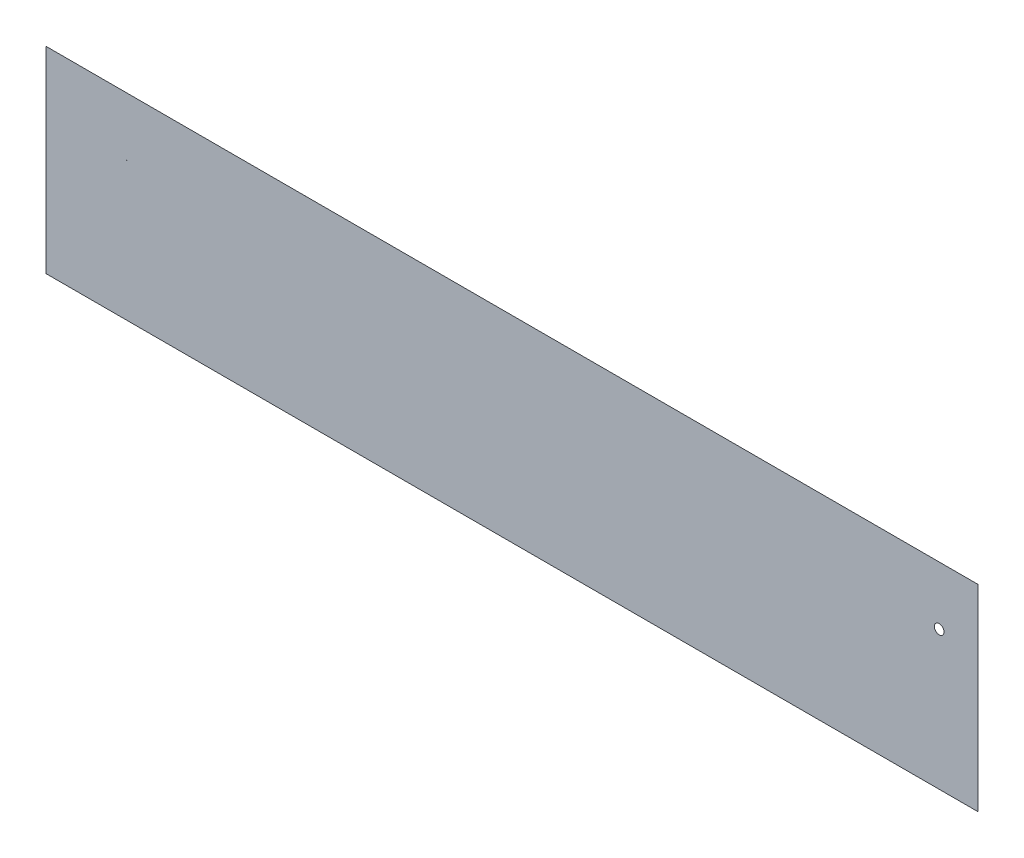
SolidWorks part; units mm, degrees
ref_plane "Front" through (0, 0, 0) normal (0, 0, 1) x (1, 0, 0)
ref_plane "Top" through (0, 0, 0) normal (0, 1, 0) x (1, 0, 0)
ref_plane "Right" through (0, 0, 0) normal (1, 0, 0) x (0, 0, -1)
sketch "Sketch1" plane through (0, 0, 0) normal (0, 0, 1) x (1, 0, 0)
  line L0 (0, 90.678) -> (609.6, 90.678) construction
  line L1 (0, 0) -> (609.6, 0)
  line L2 (0, 0) -> (0, 128.778)
  line L3 (0, 128.778) -> (609.6, 128.778)
  line L4 (609.6, 0) -> (609.6, 128.778)
  circle A0 centre (52.9747, 90.678) radius 0.1748
  circle A1 centre (584.2, 90.678) radius 3.175
  dimension "D4" = 25.4
  dimension "D5" = 6.35
  dimension "D1" = 128.778
  dimension "D2" = 609.6
  dimension "D3" = 38.1
extrude "Boss-Extrude1" add sketch "Sketch1" along normal blind 0.0001
